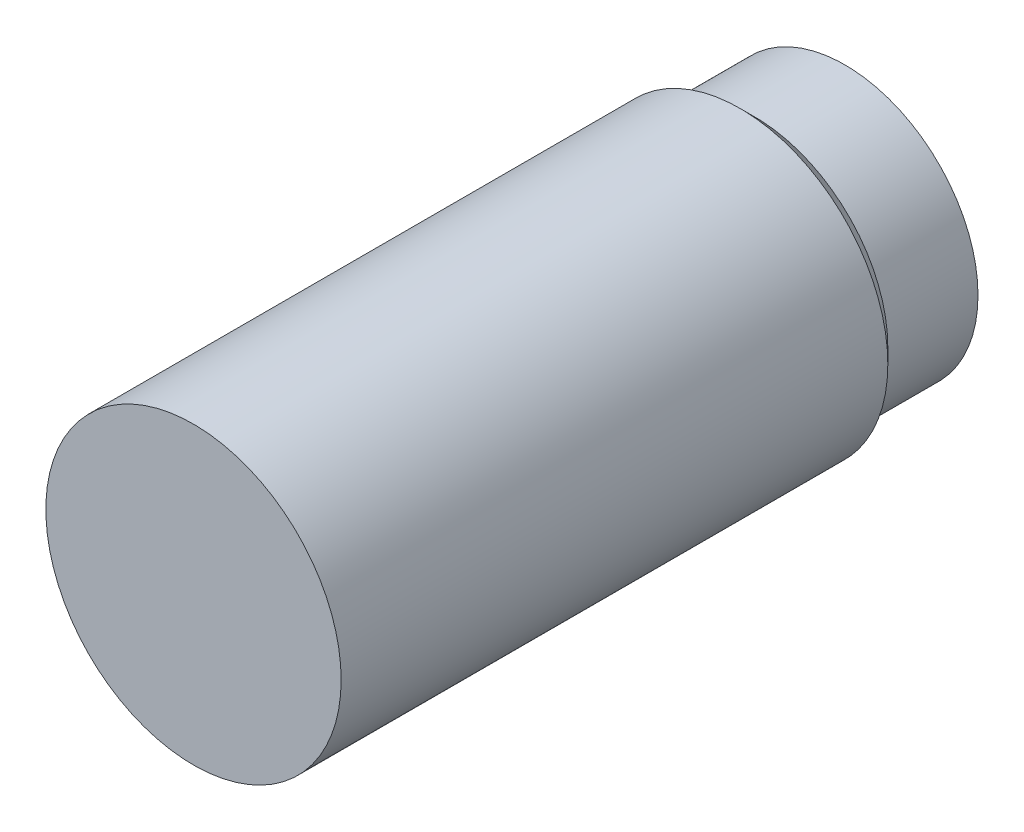
SolidWorks part; units mm, degrees
ref_plane "Front Plane" through (0, 0, 0) normal (0, 0, 1) x (1, 0, 0)
ref_plane "Top Plane" through (0, 0, 0) normal (0, 1, 0) x (1, 0, 0)
ref_plane "Right Plane" through (0, 0, 0) normal (1, 0, 0) x (0, 0, -1)
sketch "Sketch1" plane through (0, 0, 0) normal (1, 0, 0) x (0, 0, -1)
  line L0 (0, 0) -> (28.9, 0) construction
  line L1 (0, 0) -> (0, 6.55)
  line L2 (0, 6.55) -> (24.25, 6.55)
  line L3 (24.25, 6.55) -> (24.9, 5.9)
  line L4 (24.9, 5.9) -> (28.9, 5.9)
  line L5 (28.9, 5.9) -> (28.9, 0)
  line L6 (0, 0) -> (28.9, 0)
  dimension "D1" = 28.9
  dimension "D2" = 13.1
  dimension "D3" = 11.8
  dimension "D4" = 45
  dimension "D5" = 4
revolve "Revolve1" add sketch "Sketch1" angle 360 about L0
sketch "Sketch2" plane through (0, 0, -28.9) normal (0, 0, -1) x (-1, 0, 0)
  circle A0 centre (0, 0) radius 5.6
  dimension "D1" = 11.2
extrude "Cut-Extrude1" cut sketch "Sketch2" against normal blind 0.2
